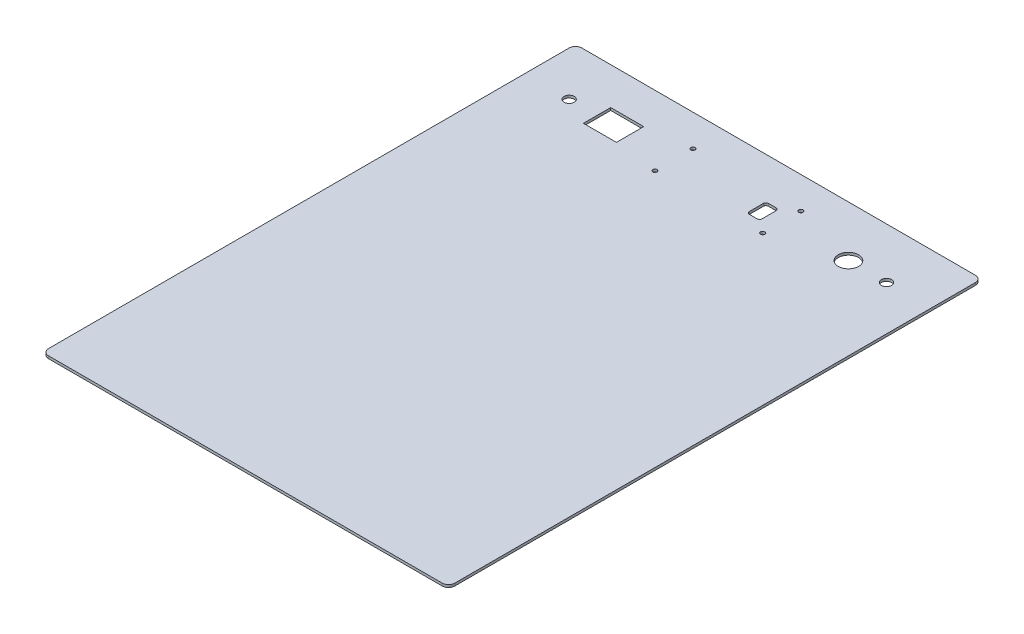
SolidWorks part; units mm, degrees
ref_plane "Front" through (0, 0, 0) normal (0, 0, 1) x (1, 0, 0)
ref_plane "Top" through (0, 0, 0) normal (0, 1, 0) x (1, 0, 0)
ref_plane "Right" through (0, 0, 0) normal (1, 0, 0) x (0, 0, -1)
sketch "Sketch1" plane through (0, 0, 0) normal (0, 1, 0) x (1, 0, 0)
  line L1 (-160, 210) -> (160, 210)
  line L2 (-160, 210) -> (-160, -210)
  line L3 (-160, -210) -> (160, -210)
  line L4 (160, 210) -> (160, -210)
  line L5 (-160, 210) -> (160, -210) construction
  line L6 (-160, -210) -> (160, 210) construction
  point P0 (0, 0)
  dimension "D1" = 320
  dimension "D2" = 420
extrude "Boss-Extrude1" add sketch "Sketch1" along normal blind 2
sketch "Sketch3" plane through (0, 2, 0) normal (0, 1, 0) x (1, 0, 0)
  line L0 (160, 210) -> (-160, 210) construction
  line L1 (-47.5, 190) -> (47.5, 190)
  line L2 (-47.5, 190) -> (-47.5, 150)
  line L3 (-47.5, 150) -> (47.5, 150)
  line L4 (47.5, 190) -> (47.5, 150)
  line L5 (-47.5, 190) -> (47.5, 150) construction
  line L6 (-47.5, 150) -> (47.5, 190) construction
  line L8 (22.5, 177.5) -> (32.5, 177.5)
  line L9 (22.5, 177.5) -> (22.5, 162.5)
  line L10 (22.5, 162.5) -> (32.5, 162.5)
  line L11 (32.5, 177.5) -> (32.5, 162.5)
  line L12 (22.5, 177.5) -> (32.5, 162.5) construction
  line L13 (22.5, 162.5) -> (32.5, 177.5) construction
  circle A0 centre (-42.5, 185) radius 1.7
  circle A1 centre (42.5, 185) radius 1.7
  circle A2 centre (42.5, 155) radius 1.7
  circle A3 centre (-42.5, 155) radius 1.7
  point P0 (0, 170)
  point P20 (27.5, 170)
  dimension "D8" = 3.4
  dimension "D1" = 95
  dimension "D2" = 40
  dimension "D3" = 20
  dimension "D4" = 5
  dimension "D5" = 5
  dimension "D6" = 5
  dimension "D7" = 5
  dimension "D9" = 15
  dimension "D10" = 10
  dimension "D11" = 15
extrude "Cut-Extrude1" cut sketch "Sketch3" against normal blind 2 contours L9 L8 L11 L10 | A1 | A0 | A3 | A2
sketch "Sketch5" plane through (0, 2, 0) normal (0, 1, 0) x (1, 0, 0)
  line L1 (-103, 180.75) -> (-77, 180.75)
  line L2 (-103, 180.75) -> (-103, 159.25)
  line L3 (-103, 159.25) -> (-77, 159.25)
  line L4 (-77, 180.75) -> (-77, 159.25)
  line L5 (-103, 180.75) -> (-77, 159.25) construction
  line L6 (-103, 159.25) -> (-77, 180.75) construction
  line L8 (-160, 210) -> (-160, -210) construction
  line L9 (160, 210) -> (-160, 210) construction
  line L10 (160, -210) -> (160, 210) construction
  circle A0 centre (-125, 170) radius 4
  circle A1 centre (95, 170) radius 8
  circle A2 centre (125, 170) radius 4
  point P0 (-90, 170)
  dimension "D5" = 8
  dimension "D7" = 16
  dimension "D8" = 8
  dimension "D1" = 26
  dimension "D2" = 21.5
  dimension "D3" = 40
  dimension "D4" = 35
  dimension "D6" = 35
  dimension "D9" = 35
  dimension "D10" = 30
extrude "Cut-Extrude2" cut sketch "Sketch5" against normal blind 2
fillet "Fillet1" radius 5 4 edges at (160, 1, 210) (-160, 1, 210) (-160, 1, -210) (160, 1, -210)
fillet "Fillet2" radius 2 4 edges at (22.5, 1, -162.5) (32.5, 1, -162.5) (32.5, 1, -177.5) (22.5, 1, -177.5)
